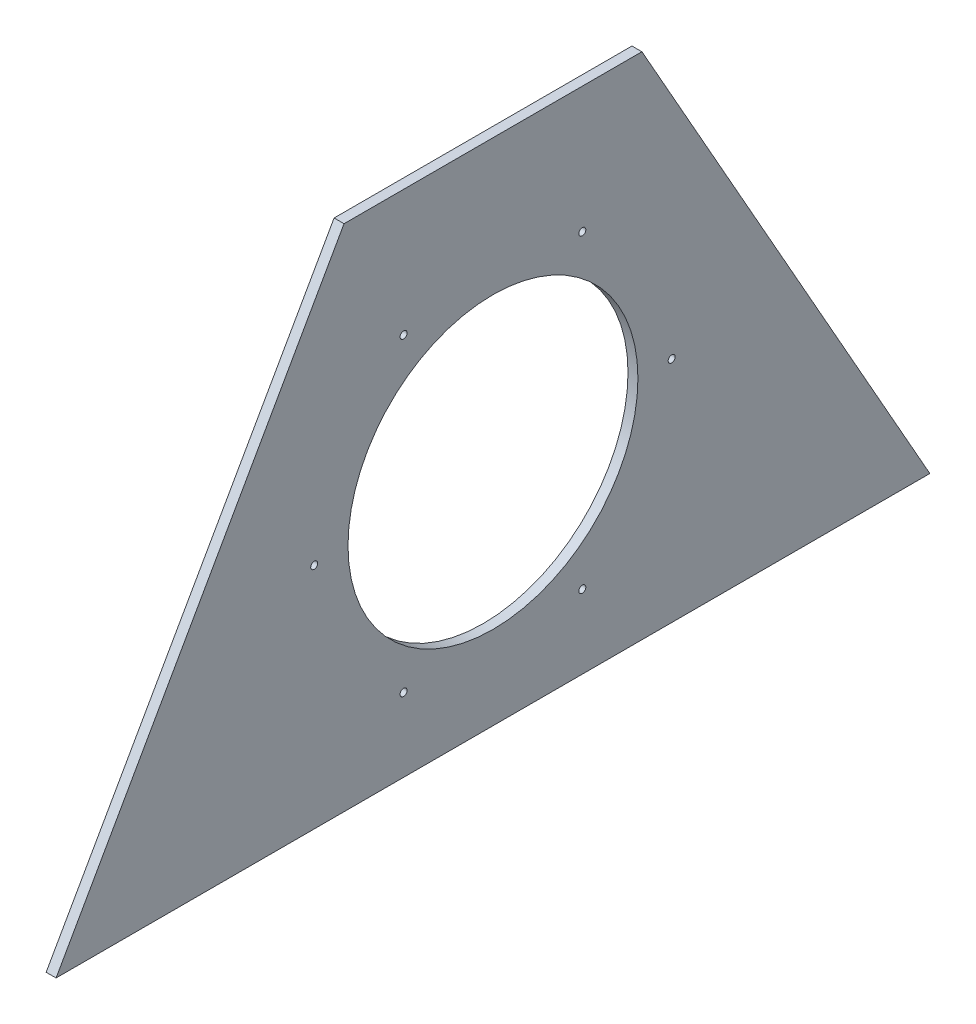
SolidWorks part; units mm, degrees
material "Pine"
ref_plane "Front Plane" through (0, 0, 0) normal (0, 0, 1) x (1, 0, 0)
ref_plane "Top Plane" through (0, 0, 0) normal (0, 1, 0) x (1, 0, 0)
ref_plane "Right Plane" through (0, 0, 0) normal (1, 0, 0) x (0, 0, -1)
sketch "Sketch1" plane through (0, 0, 0) normal (1, 0, 0) x (0, 0, -1)
  line L1 (0, 0) -> (558.8, 0)
  line L2 (0, 0) -> (184.15, 325.6855)
  line L3 (184.15, 325.6855) -> (374.65, 325.6855)
  line L4 (558.8, 0) -> (374.65, 325.6855)
  point P5 (279.4, 325.6855)
  point P6 (279.4, 0)
  dimension "D1" = 558.8
  dimension "D2" = 374.142
  dimension "D3" = 190.5
extrude "Boss-Extrude1" add sketch "Sketch1" along normal blind 6.35
sketch "Sketch2" plane through (6.35, 0, 0) normal (1, 0, 0) x (0, 0, -1)
  line L0 (0, 0) -> (558.8, 0) construction
  line L1 (279.4, 325.6855) -> (279.4, 0) construction
  line L2 (374.65, 325.6855) -> (184.15, 325.6855) construction
  line L3 (0, 0) -> (558.8, 0) construction
  circle A0 centre (279.4, 146.05) radius 92.71
  point P5 (279.4, 0)
  dimension "D1" = 185.42
  dimension "D2" = 146.05
extrude "Cut-Extrude1" cut sketch "Sketch2" against normal through all
hole_wizard "#8 Clearance Hole1" positions "Sketch3" profile "Sketch4" hole size "#8" standard "ANSI Inch"
sketch "Sketch3" plane through (0, 0, 0) normal (-1, 0, 0) x (0, 0, 1)
  line L1 (-222.25, 47.0633) -> (-165.1, 146.05)
  line L2 (-165.1, 146.05) -> (-222.25, 245.0367)
  line L3 (-222.25, 245.0367) -> (-336.55, 245.0367)
  line L4 (-336.55, 245.0367) -> (-393.7, 146.05)
  line L5 (-393.7, 146.05) -> (-336.55, 47.0633)
  line L6 (-336.55, 47.0633) -> (-222.25, 47.0633)
  circle A12 centre (-279.4, 146.05) radius 98.9867 construction
  point P46 (-222.25, 245.0367)
  point P49 (-165.1, 146.05)
  point P52 (-222.25, 47.0633)
  point P55 (-336.55, 47.0633)
  point P58 (-393.7, 146.05)
  point P61 (-336.55, 245.0367)
  dimension "D1" = 114.3
sketch "Sketch4" plane through (0, 245.0367, -336.55) normal (0, 1, 0) x (0, 0, 1)
  line L0 (0, 0) -> (0, 26.7507)
  line L1 (0, 26.7507) -> (2.2479, 25.4)
  line L2 (2.2479, 25.4) -> (2.2479, 0)
  line L5 (2.2479, 0) -> (0, 0)
  line L10 (0, 26.7507) -> (-2.2479, 25.4) construction
  line L11 (0, -6.35) -> (0, 107.95) construction
  dimension "Hole Dia." = 4.4958
  dimension "Hole Depth" = 25.4
  dimension "Drill Angle" = 118
